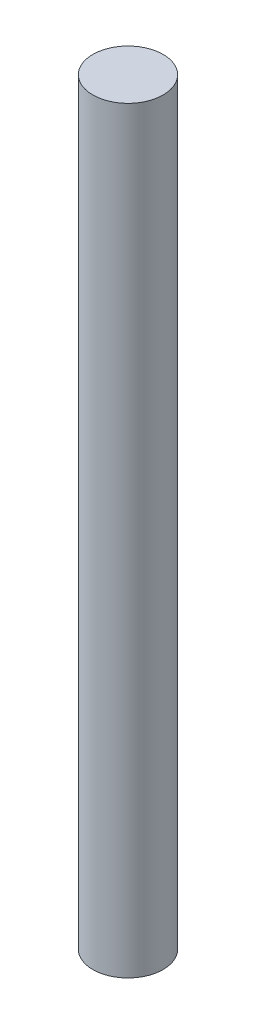
SolidWorks part; units mm, degrees
ref_plane "Front Plane" through (0, 0, 0) normal (0, 0, 1) x (1, 0, 0)
ref_plane "Top Plane" through (0, 0, 0) normal (0, 1, 0) x (1, 0, 0)
ref_plane "Right Plane" through (0, 0, 0) normal (1, 0, 0) x (0, 0, -1)
sketch "Sketch1" plane through (0, 0, 0) normal (0, 1, 0) x (1, 0, 0)
  circle A0 centre (0, 0) radius 4
  dimension "D1" = 8
extrude "Boss-Extrude1" add sketch "Sketch1" along normal blind 95
sketch "Sketch2" plane through (0, 95, 0) normal (0, 1, 0) x (1, 0, 0)
  circle A0 centre (0, 0) radius 4 construction
  circle A1 centre (0, 0) radius 4
extrude "Cut-Extrude1" cut sketch "Sketch2" against normal blind 8.75
